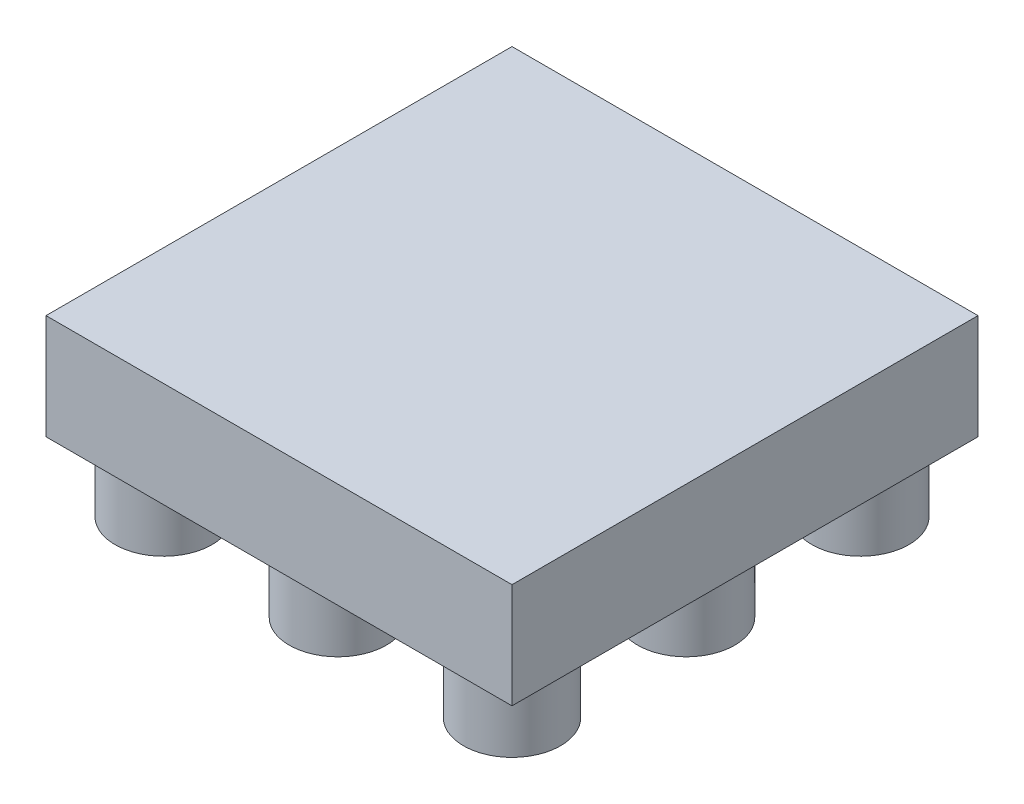
SolidWorks part; units mm, degrees
ref_plane "Front Plane" through (0, 0, 0) normal (0, 0, 1) x (1, 0, 0)
ref_plane "Top Plane" through (0, 0, 0) normal (0, 1, 0) x (1, 0, 0)
ref_plane "Right Plane" through (0, 0, 0) normal (1, 0, 0) x (0, 0, -1)
ref_plane "Plane2" through (0, 1.5875, 0) normal (0, 1, 0) x (-1, 0, 0)
sketch "Sketch3" plane through (0, 1.5875, 0) normal (0, 1, 0) x (-1, 0, 0)
  line L1 (-7.01, -15.61) -> (-17.71, -15.61)
  line L2 (-7.01, -15.61) -> (-7.01, -26.31)
  line L3 (-7.01, -26.31) -> (-17.71, -26.31)
  line L4 (-17.71, -15.61) -> (-17.71, -26.31)
extrude "Boss-Extrude2" add sketch "Sketch3" along normal blind 2.41
sketch "Sketch5" plane through (0, 1.5875, 0) normal (0, -1, 0) x (1, 0, 0)
  circle A0 centre (16.36, -24.96) radius 1.115
  circle A1 centre (12.36, -24.96) radius 1.115
  circle A2 centre (8.36, -24.96) radius 1.115
  circle A3 centre (16.36, -20.96) radius 1.115
  circle A4 centre (12.36, -20.96) radius 1.115
  circle A5 centre (8.36, -20.96) radius 1.115
  circle A6 centre (16.36, -16.96) radius 1.115
  circle A7 centre (12.36, -16.96) radius 1.115
  circle A8 centre (8.36, -16.96) radius 1.115
  dimension "D1" = 3
  dimension "D2" = 3
extrude "Boss-Extrude3" add sketch "Sketch5" along normal blind 1.5875
sketch "Sketch6" plane through (0, 3.9975, 0) normal (0, 1, 0) x (1, 0, 0)
  line L1 (-0.5, 15) -> (23.5, 15)
  line L2 (-0.5, 15) -> (-0.5, 26.5)
  line L3 (-0.5, 26.5) -> (23.5, 26.5)
  line L4 (23.5, 15) -> (23.5, 26.5)
extrude "Boss-Extrude4" [suppressed] add sketch "Sketch6" along normal blind 1.5875 separate body
sketch "Sketch7" plane through (17.71, 0, 0) normal (1, 0, 0) x (0, 0, -1)
  line L0 (15.61, 3.9975) -> (26.31, 3.9975) construction
  line L1 (15.61, 2.1895) -> (22.6914, 2.1895)
  line L2 (15.61, 2.1895) -> (15.61, 3.9975)
  line L3 (15.61, 3.9975) -> (22.6914, 3.9975)
  line L4 (22.6914, 2.1895) -> (22.6914, 3.9975)
  line L5 (15.61, 3.9975) -> (15.61, 1.5875) construction
extrude "Boss-Extrude5" [suppressed] add sketch "Sketch7" along normal blind 5.79 separate body
sketch "Sketch8" [suppressed] plane through (7.01, 0, 0) normal (-1, 0, 0) x (0, 0, 1)
  line L1 (-22.6914, 2.1895) -> (-15.61, 2.1895)
  line L2 (-22.6914, 2.1895) -> (-22.6914, 3.9975)
  line L3 (-22.6914, 3.9975) -> (-15.61, 3.9975)
  line L4 (-15.61, 2.1895) -> (-15.61, 3.9975)
extrude "Boss-Extrude6" [suppressed] add sketch "Sketch8" along normal blind 7.51 separate body
